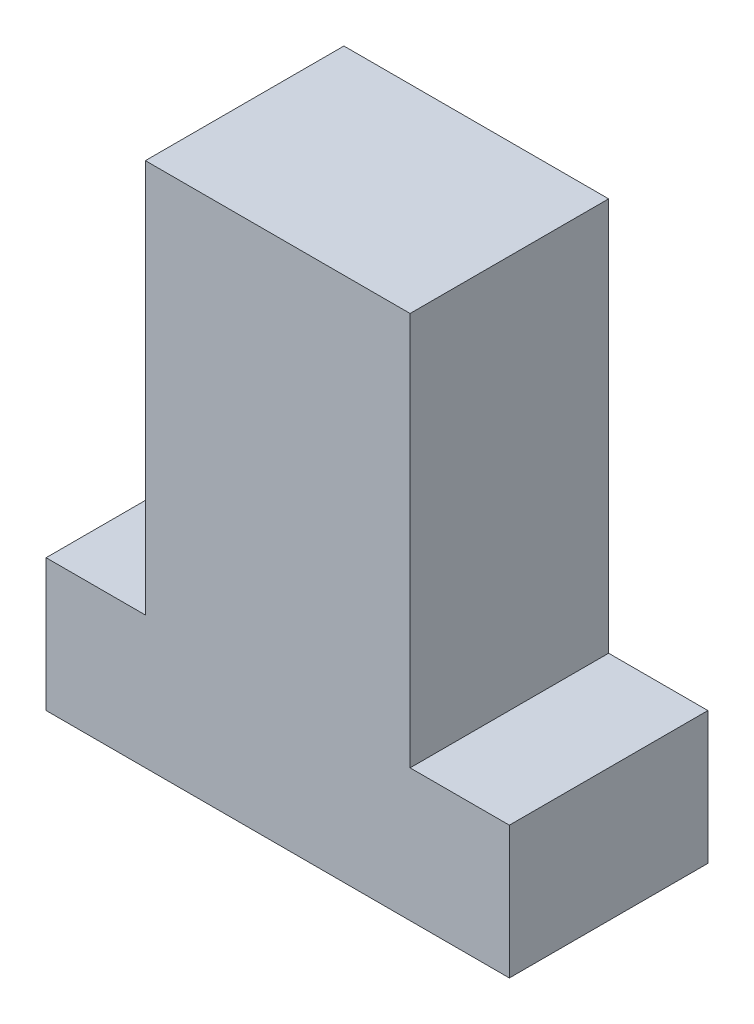
SolidWorks part; units mm, degrees
material "Pine"
ref_plane "Front Plane" through (0, 0, 0) normal (0, 0, 1) x (1, 0, 0)
ref_plane "Top Plane" through (0, 0, 0) normal (0, 1, 0) x (1, 0, 0)
ref_plane "Right Plane" through (0, 0, 0) normal (1, 0, 0) x (0, 0, -1)
sketch "Sketch1" plane through (0, 0, 0) normal (0, 0, 1) x (1, 0, 0)
  line L1 (-35, -10) -> (35, -10)
  line L2 (-35, -10) -> (-35, 10)
  line L3 (-35, 10) -> (35, 10)
  line L4 (35, -10) -> (35, 10)
  line L5 (-35, -10) -> (35, 10) construction
  line L6 (-35, 10) -> (35, -10) construction
  line L7 (-20, 10) -> (20, 10)
  line L8 (-20, 10) -> (-20, 69.46)
  line L9 (-20, 69.46) -> (20, 69.46)
  line L10 (20, 10) -> (20, 69.46)
  line L11 (-20, 10) -> (20, 69.46) construction
  line L12 (-20, 69.46) -> (20, 10) construction
  point P1 (0, 0)
  point P6 (0, 39.73)
  dimension "D1" = 70
  dimension "D2" = 20
  dimension "D3" = 40
  dimension "D4" = 59.46
  dimension "D5" = 29.73
  dimension "D6" = 35
extrude "Boss-Extrude1" add sketch "Sketch1" along normal blind 30 contours L3 L10 L9 L8 | L1 L4 L3 L2
sketch "Sketch2" plane through (0, 10, 0) normal (0, 1, 0) x (1, 0, 0)
  line L0 (0, 0) -> (0, -30) construction
  line L1 (-20, -30) -> (20, -30) construction
  line L2 (35, -30) -> (35, 0) construction
  line L3 (20, 0) -> (35, 0) construction
  line L4 (20, -30) -> (35, -30) construction
  point P0 (27, -10)
  point P1 (27, -20)
  point P13 (-27, -20)
  point P14 (-27, -10)
  dimension "D1" = 8
  dimension "D2" = 8
  dimension "D3" = 10
  dimension "D4" = 10
